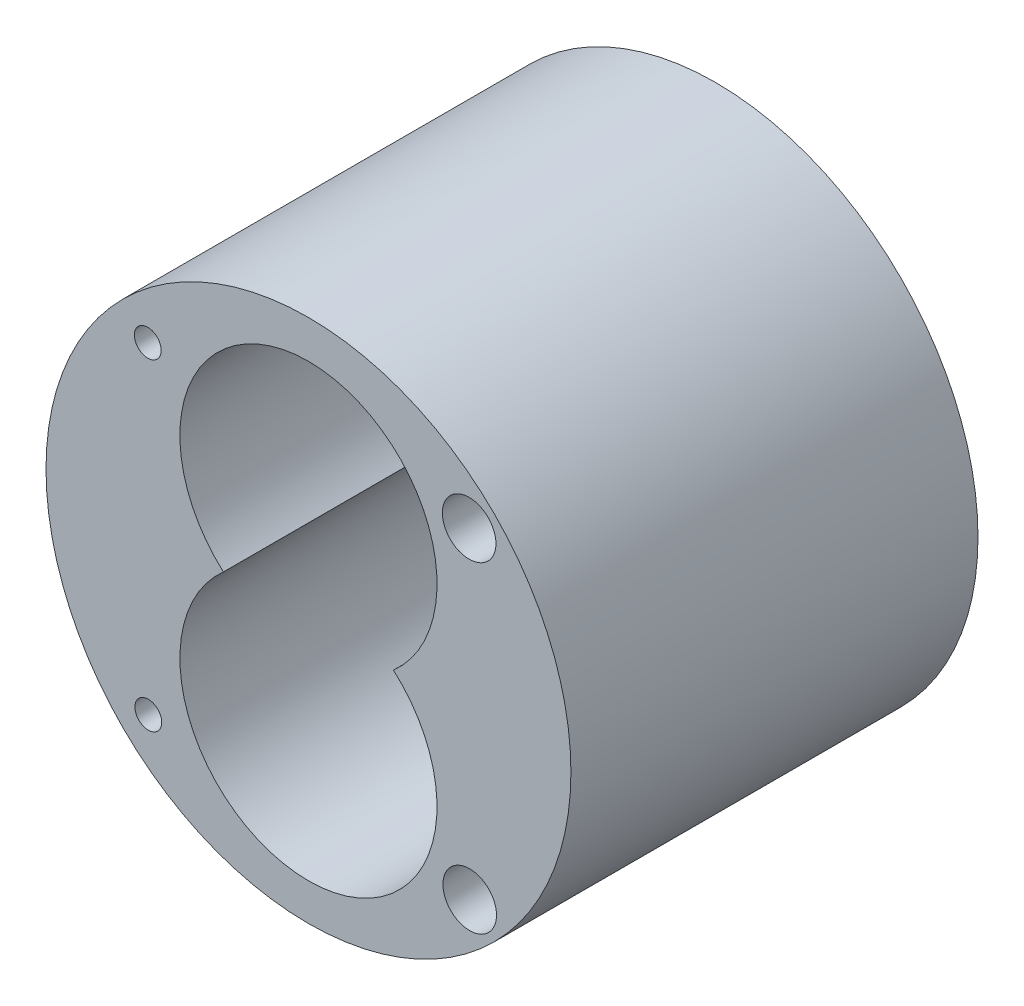
SolidWorks part; units mm, degrees
ref_plane "Front Plane" through (0, 0, 0) normal (0, 0, 1) x (1, 0, 0)
ref_plane "Top Plane" through (0, 0, 0) normal (0, 1, 0) x (1, 0, 0)
ref_plane "Right Plane" through (0, 0, 0) normal (1, 0, 0) x (0, 0, -1)
sketch "Sketch1" plane through (0, 0, 0) normal (0, 0, 1) x (1, 0, 0)
  line L0 (-30, 42.4732) -> (-30, -42.643) construction
  line L1 (30, 42.4732) -> (30, -42.643) construction
  line L2 (-50.8645, 17.9151) -> (61.8868, 17.9151) construction
  line L3 (-48.2392, 29.9151) -> (70.5919, 29.9151) construction
  line L4 (-50.8645, -30.0849) -> (58.7088, -30.0849) construction
  line L5 (-49.8973, -0.0849) -> (61.8868, -0.0849) construction
  line L6 (0, 48.4148) -> (0, -47.6173) construction
  line L7 (-51.5974, -18.0849) -> (61.8868, -18.0849) construction
  line L9 (-48.8826, -0.0849) -> (-49, 0)
  circle A0 centre (0, 0) radius 49
  circle A1 centre (-30, 29.9151) radius 2.5
  circle A2 centre (30, 29.9151) radius 5
  circle A3 centre (-29.8986, -30.1801) radius 2.5
  circle A4 centre (30.1014, -30.0897) radius 5
  arc A6 (-15.8745, -0.0849) -> (15.8745, -0.0849) centre (0, -18.0849) ccw
  arc A10 (15.8745, -0.0849) -> (-15.8745, -0.0849) centre (0, 17.9151) ccw
  dimension "D5" = 98
  dimension "D6" = 5
  dimension "D7" = 10
  dimension "D8" = 18
  dimension "D12" = 48
  dimension "D1" = 30
  dimension "D2" = 30
  dimension "D3" = 30
  dimension "D4" = 30
  dimension "D9" = 18
extrude "Boss-Extrude1" add sketch "Sketch1" along normal blind 76
